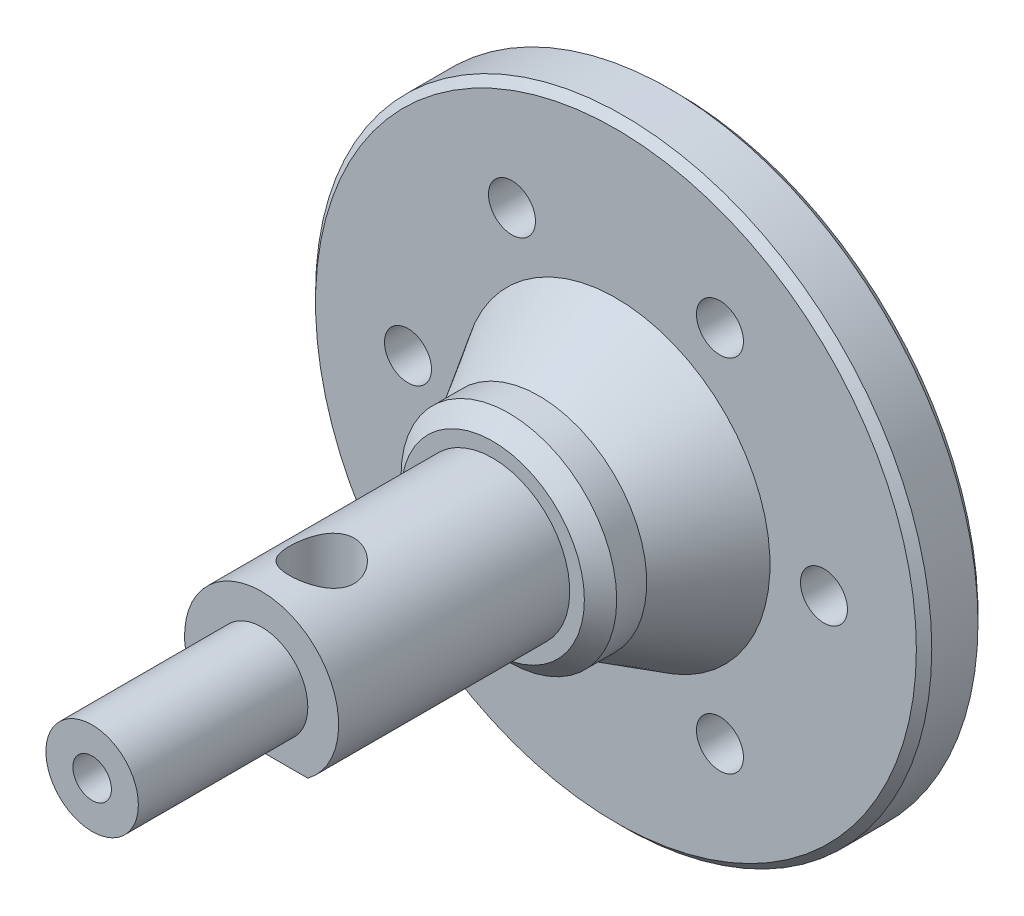
SolidWorks part; units mm, degrees
material "6063-T5"
ref_plane "前视基准面" through (0, 0, 0) normal (0, 0, 1) x (1, 0, 0)
ref_plane "上视基准面" through (0, 0, 0) normal (0, 1, 0) x (1, 0, 0)
ref_plane "右视基准面" through (0, 0, 0) normal (1, 0, 0) x (0, 0, -1)
other "Configuration Table"
sketch "草图1" plane through (0, 0, 0) normal (0, 0, 1) x (1, 0, 0)
  circle A0 centre (0, 0) radius 20
  dimension "D1" = 40
extrude "凸台-拉伸1" add sketch "草图1" along normal blind 5
sketch "草图2" plane through (0, 0, 5) normal (0, 0, 1) x (1, 0, 0)
  circle A0 centre (0, 0) radius 13.5 construction
  circle A1 centre (13.5, 0) radius 1.525
  circle A2 centre (6.75, -11.6913) radius 1.525
  circle A3 centre (-6.75, -11.6913) radius 1.525
  circle A4 centre (-13.5, 0) radius 1.525
  circle A5 centre (-6.75, 11.6913) radius 1.525
  circle A6 centre (6.75, 11.6913) radius 1.525
  point P17 (0, 0)
  dimension "D1" = 27
  dimension "D2" = 3.05
  dimension "D3" = 6
extrude "切除-拉伸1" cut sketch "草图2" against normal blind 5
sketch "草图3" plane through (0, 0, 5) normal (0, 0, 1) x (1, 0, 0)
  circle A0 centre (0, 0) radius 7
  dimension "D1" = 14
extrude "凸台-拉伸2" add sketch "草图3" along normal blind 4
sketch "草图4" plane through (0, 0, 9) normal (0, 0, 1) x (1, 0, 0)
  circle A1 centre (0, 0) radius 5
  dimension "D1" = 10
extrude "凸台-拉伸3" add sketch "草图4" along normal blind 15
chamfer "倒角2" distance 1.05 angle 45 1 edges at (7, 0, 9)
sketch "草图6" plane through (0, 0, 24) normal (0, 0, 1) x (1, 0, 0)
  line L0 (-3, -4) -> (3, -4)
  circle A0 centre (0, 0) radius 5 construction
  circle A1 centre (0, 0) radius 5 construction
  arc A2 (-3, -4) -> (3, -4) centre (0, 0) ccw
  dimension "D1" = 4
extrude "切除-拉伸2" cut sketch "草图6" against normal blind 15
sketch "草图7" plane through (0, 0, 24) normal (0, 0, 1) x (1, 0, 0)
  circle A0 centre (0, 0) radius 3
  dimension "D1" = 6
extrude "凸台-拉伸4" add sketch "草图7" along normal blind 10
sketch "草图8" plane through (0, 0, 5) normal (0, 0, 1) x (1, 0, 0)
  circle A0 centre (0, 0) radius 7
  circle A1 centre (0, 0) radius 20
  dimension "D1" = 14
  dimension "D2" = 40
extrude "切除-拉伸3" cut sketch "草图8" against normal blind 1
sketch "草图9" plane through (0, 0, 0) normal (0, 0, -1) x (-1, 0, 0)
  circle A0 centre (6.75, 11.6913) radius 1.525 construction
  circle A1 centre (0, 0) radius 20
  circle A2 centre (0, 0) radius 20
  circle A3 centre (13.5, 0) radius 1.525 construction
  circle A4 centre (6.75, -11.6913) radius 1.525 construction
  circle A5 centre (-6.75, -11.6913) radius 1.525 construction
  circle A6 centre (-13.5, 0) radius 1.525 construction
  circle A7 centre (-6.75, 11.6913) radius 1.525 construction
  circle A8 centre (6.75, 11.6913) radius 1.525
  circle A9 centre (13.5, 0) radius 1.525
  circle A10 centre (6.75, -11.6913) radius 1.525
  circle A11 centre (-6.75, -11.6913) radius 1.525
  circle A12 centre (-13.5, 0) radius 1.525
  circle A13 centre (-6.75, 11.6913) radius 1.525
  dimension "D1" = 0
extrude "凸台-拉伸5" add sketch "草图9" along normal blind 3
sketch "草图10" plane through (0, 0, 4) normal (0, 0, 1) x (1, 0, 0)
  circle A0 centre (0, 0) radius 7
  circle A1 centre (0, 0) radius 20
  dimension "D1" = 14
  dimension "D2" = 40
extrude "切除-拉伸4" cut sketch "草图10" against normal blind 3
sketch "草图11" plane through (0, 0, 34) normal (0, 0, 1) x (1, 0, 0)
  circle A0 centre (0, 0) radius 3
  dimension "D1" = 6
extrude "凸台-拉伸6" add sketch "草图11" along normal blind 1
hole_wizard "M3 螺纹孔1" positions "3D草图1" profile "草图13" tap size "M3" standard "GB"
sketch3d "3D草图1"
  line L0 (0, 0, 35) -> (0, 0, 24) construction
  point P0 (0, 0, 35)
sketch "草图13" plane through (0, 0, 35) normal (1, 0, 0) x (0, -1, 0)
  line L0 (0, 0) -> (0, 5.7511)
  line L1 (0, 5.7511) -> (1.25, 5)
  line L2 (1.25, 5) -> (1.25, 0)
  line L5 (1.25, 0) -> (0, 0)
  line L10 (0, 5.7511) -> (-1.25, 5) construction
  line L11 (0, -6.35) -> (0, 107.95) construction
  dimension "螺纹孔钻头直径" = 2.5
  dimension "螺纹孔钻头深度" = 5
  dimension "导头角度" = 118
cosmetic thread "孔螺蚊线1" parameters "D1"=6, "D2"=3
chamfer "倒角3" distance 0.5 angle 45 2 edges at (-20, 0, -3) (20, 0, 1)
sketch "草图14" plane through (0, -4, 0) normal (0, -1, 0) x (1, 0, 0)
  line L0 (3, 24) -> (-3, 24) construction
  circle A0 centre (0, 20.1) radius 1.5
  dimension "D2" = 3
  dimension "D1" = 3.9
hole_wizard "M5 螺纹孔1" positions "3D草图3" profile "草图16" tap size "M5" standard "GB" end condition through all
sketch3d "3D草图3"
  point P0 (0, -4, 20.1)
sketch "草图16" plane through (0, -4, 20.1) normal (1, 0, 0) x (0, 0, -1)
  line L0 (0, 0) -> (0, 24)
  line L1 (0, 24) -> (2.1, 24)
  line L2 (2.1, 24) -> (2.1, 0)
  line L5 (2.1, 0) -> (0, 0)
  line L11 (0, -6.35) -> (0, 107.95) construction
  dimension "通孔螺纹孔钻头直径" = 4.2
  dimension "通孔螺纹孔钻头深度" = 24
cosmetic thread "孔螺蚊线2" parameters "D2"=5
sketch "草图17" plane through (0, 0, 0) normal (1, 0, 0) x (0, 0, -1)
  line L0 (-6, -7) -> (-1, -10)
  line L1 (-7.95, -7) -> (-1, -7) construction
  line L2 (-1, 19.5) -> (-1, -19.5) construction
  dimension "D1" = 3
  dimension "D2" = 5
chamfer "倒角4" distance 1 angle 45 1 edges at (7, 0, 1)
sketch "草图18" plane through (0, 0, 0) normal (1, 0, 0) x (0, 0, -1)
  line L0 (-1, 10) -> (-6.8333, 6.5)
  line L3 (-6.8333, 6.5) -> (-1, 6.5)
  line L5 (-1, 6.5) -> (-1, 10)
  line L7 (0, 0) -> (-5.8333, 0) construction
  line L8 (-1, 19.5) -> (-1, -19.5) construction
  dimension "D1" = 3.5
  dimension "D2" = 6.5
  dimension "D3" = 5.8333
revolve "旋转1" [suppressed] add sketch "草图18" angle 360 about L7
sketch "草图20" plane through (0, 0, 24) normal (0, 0, 1) x (1, 0, 0)
  circle A0 centre (0, 0) radius 4
  dimension "D1" = 8
sketch "草图22" plane through (0, 0, 0) normal (0, 1, 0) x (1, 0, 0)
  line L0 (6.5, -6.8333) -> (10, -1)
  line L1 (10, -1) -> (6.5, -1)
  line L2 (-8, -1) -> (8, -1) construction
  line L3 (6.5, -1) -> (6.5, -6.8333)
  line L4 (-19.5, -1) -> (19.5, -1) construction
  line L8 (0, 0) -> (0, -6.8333) construction
  dimension "D1" = 3.5
  dimension "D2" = 6.5
  dimension "D3" = 5.8333
revolve "旋转2" add sketch "草图22" angle 360 about L8
